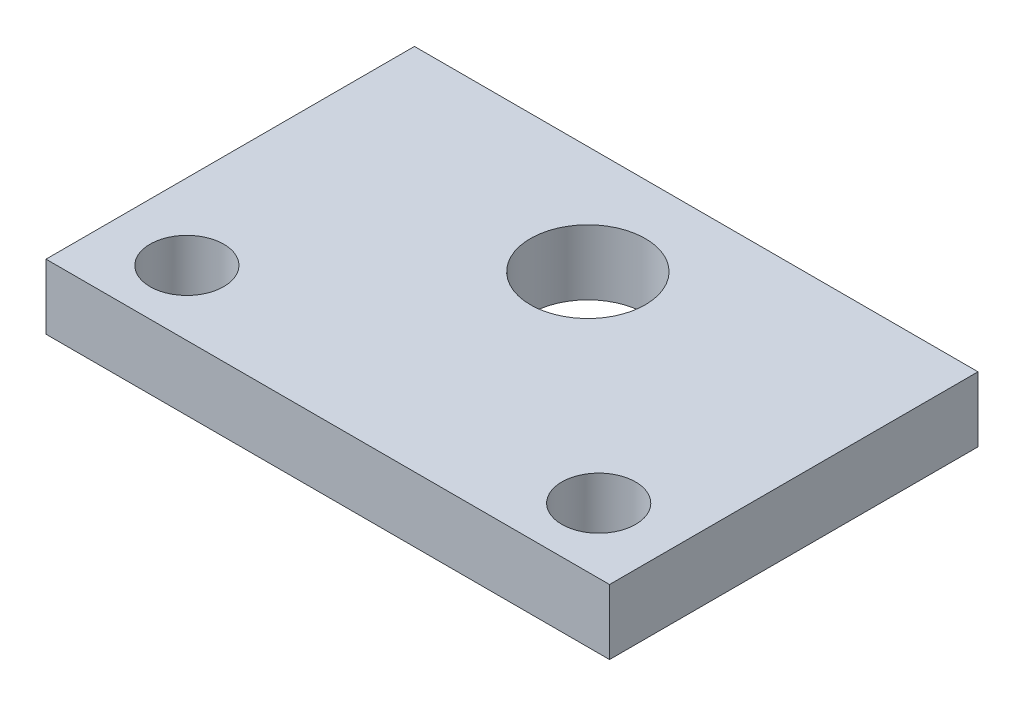
SolidWorks part; units mm, degrees
ref_plane "Front" through (0, 0, 0) normal (0, 0, 1) x (1, 0, 0)
ref_plane "Top" through (0, 0, 0) normal (0, 1, 0) x (1, 0, 0)
ref_plane "Right" through (0, 0, 0) normal (1, 0, 0) x (0, 0, -1)
sketch "Esboço1" plane through (0, 0, 0) normal (0, 1, 0) x (1, 0, 0)
  line L1 (0, 0) -> (26, 0)
  line L2 (0, 0) -> (0, 17)
  line L3 (0, 17) -> (26, 17)
  line L4 (26, 0) -> (26, 17)
  line L5 (0, 0) -> (26, 17) construction
  line L6 (0, 17) -> (26, 0) construction
  circle A1 centre (13, 12) radius 2.65
  point P6 (0, 0)
  point P8 (13, 17)
  point P9 (13, 12)
  dimension "D3" = 12
  dimension "D4" = 5.3
  dimension "D1" = 26
  dimension "D2" = 5
extrude "Ressalto-extrusão1" add sketch "Esboço1" along normal blind 3
sketch "Esboço2" plane through (0, 3, 0) normal (0, 1, 0) x (1, 0, 0)
  line L0 (3.5, 3) -> (22.5, 3) construction
  line L1 (0, 0) -> (26, 0) construction
  circle A0 centre (3.5, 3) radius 1.7
  circle A1 centre (22.5, 3) radius 1.7
  circle A2 centre (13, 12) radius 2.65 construction
  circle A3 centre (13, 12) radius 2.65 construction
  point P7 (0, 0)
  point P8 (13, 3)
  dimension "D1" = 3.4
  dimension "D2" = 19
  dimension "D3" = 3
extrude "Corte-extrusão1" cut sketch "Esboço2" against normal blind 10
